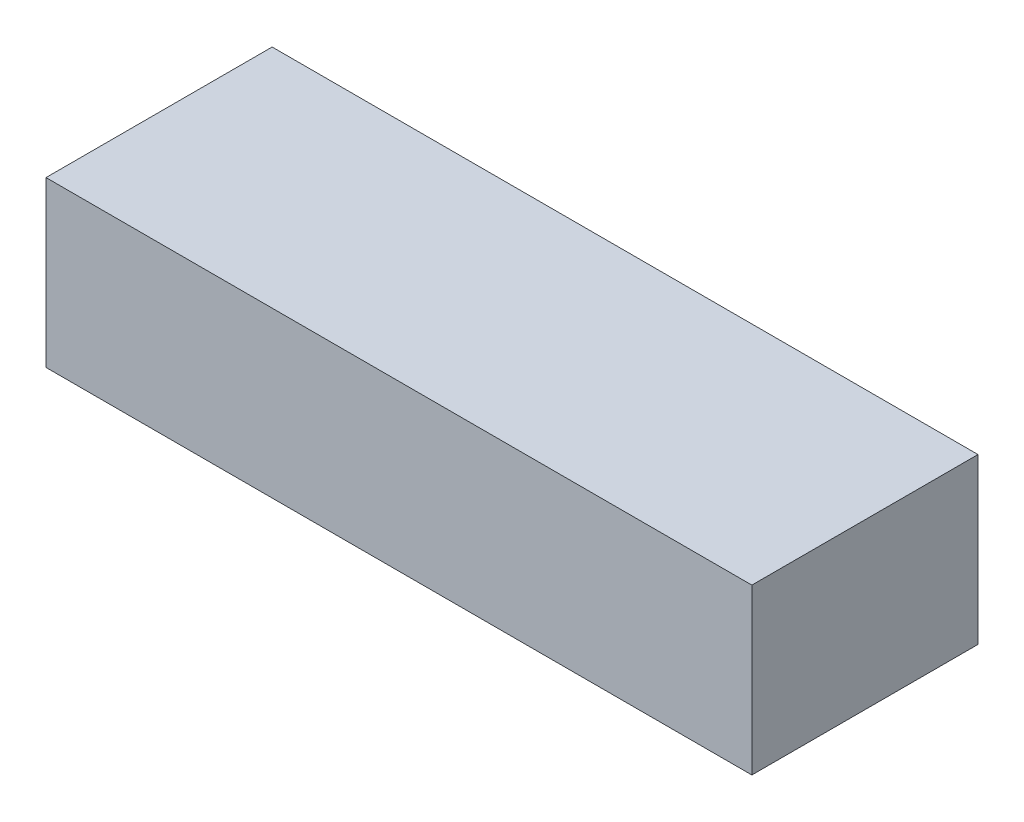
SolidWorks part; units mm, degrees
material "ABS"
ref_plane "Front Plane" through (0, 0, 0) normal (0, 0, 1) x (1, 0, 0)
ref_plane "Top Plane" through (0, 0, 0) normal (0, 1, 0) x (1, 0, 0)
ref_plane "Right Plane" through (0, 0, 0) normal (1, 0, 0) x (0, 0, -1)
sketch "Sketch1" plane through (0, 0, 0) normal (0, 1, 0) x (1, 0, 0)
  line L1 (-51.5, -16.5) -> (51.5, -16.5)
  line L2 (-51.5, -16.5) -> (-51.5, 16.5)
  line L3 (-51.5, 16.5) -> (51.5, 16.5)
  line L4 (51.5, -16.5) -> (51.5, 16.5)
  line L5 (-51.5, -16.5) -> (51.5, 16.5) construction
  line L6 (-51.5, 16.5) -> (51.5, -16.5) construction
  point P0 (0, 0)
extrude "Boss-Extrude1" add sketch "Sketch1" along normal blind 24
